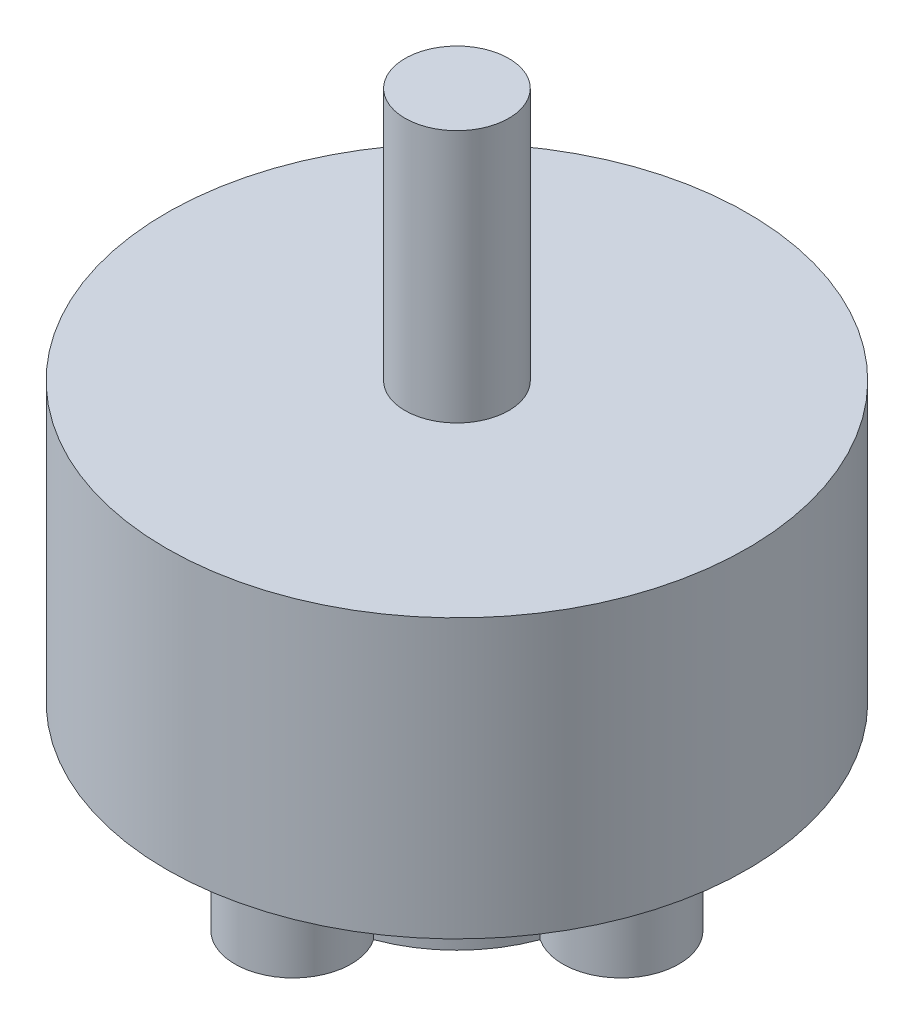
SolidWorks part; units mm, degrees
ref_plane "Front Plane" through (0, 0, 0) normal (0, 0, 1) x (1, 0, 0)
ref_plane "Top Plane" through (0, 0, 0) normal (0, 1, 0) x (1, 0, 0)
ref_plane "Right Plane" through (0, 0, 0) normal (1, 0, 0) x (0, 0, -1)
sketch "Sketch1" plane through (0, 0, 0) normal (0, 1, 0) x (1, 0, 0)
  circle A0 centre (0, 0) radius 14
  dimension "D1" = 28
extrude "Boss-Extrude1" add sketch "Sketch1" along normal blind 13.4
sketch "Sketch2" plane through (0, 13.4, 0) normal (0, 1, 0) x (1, 0, 0)
  circle A0 centre (0, 0) radius 2.5
  dimension "D1" = 5
extrude "Boss-Extrude2" add sketch "Sketch2" along normal blind 12.2
sketch "Sketch3" plane through (0, 0, 0) normal (0, -1, 0) x (1, 0, 0)
  circle A0 centre (0, 0) radius 6.75
  arc A1 (0.4526, 6.7348) -> (-0.4526, 6.7348) centre (0, 7.9) ccw
  arc A2 (2.3235, 6.3375) -> (-2.3235, 6.3375) centre (0, 7.9) ccw
  arc A3 (6.3375, -2.3235) -> (6.3375, 2.3235) centre (7.9, 0) ccw
  arc A4 (6.7348, -0.4526) -> (6.7348, 0.4526) centre (7.9, 0) ccw
  arc A5 (-2.3235, -6.3375) -> (2.3235, -6.3375) centre (0, -7.9) ccw
  arc A6 (-0.4526, -6.7348) -> (0.4526, -6.7348) centre (0, -7.9) ccw
  arc A7 (-6.3375, 2.3235) -> (-6.3375, -2.3235) centre (-7.9, 0) ccw
  arc A8 (-6.7348, 0.4526) -> (-6.7348, -0.4526) centre (-7.9, 0) ccw
  point P26 (0, 0)
  dimension "D1" = 7.9
  dimension "D2" = 13.5
  dimension "D3" = 2.5
  dimension "D4" = 5.6
  dimension "D5" = 4
extrude "Boss-Extrude3" add sketch "Sketch3" along normal blind 5.6 contours A0 | A8 A0 A7 | A0 A2 A1 | A6 A0 A5 | A4 A0 A3
